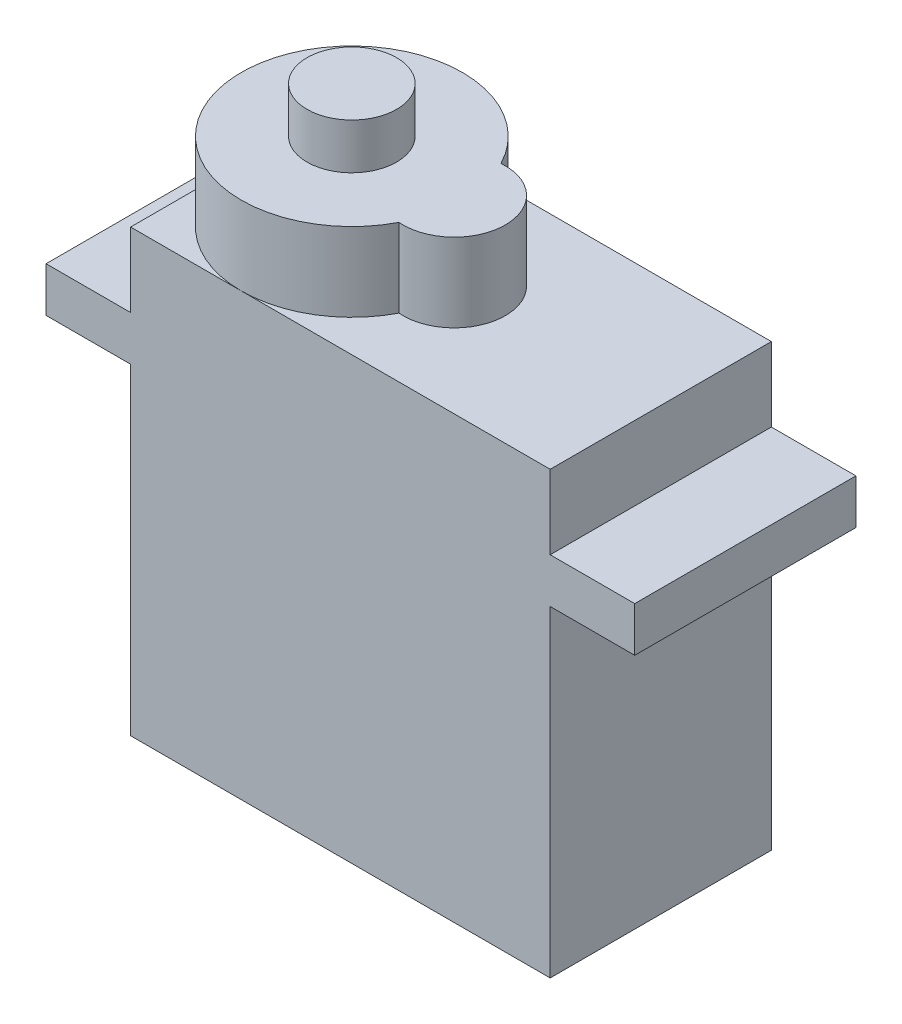
SolidWorks part; units mm, degrees
ref_plane "Front Plane" through (0, 0, 0) normal (0, 0, 1) x (1, 0, 0)
ref_plane "Top Plane" through (0, 0, 0) normal (0, 1, 0) x (1, 0, 0)
ref_plane "Right Plane" through (0, 0, 0) normal (1, 0, 0) x (0, 0, -1)
sketch "Sketch1" plane through (0, 0, 0) normal (0, 1, 0) x (1, 0, 0)
  line L1 (11.475, 6.05) -> (-11.475, 6.05)
  line L2 (11.475, 6.05) -> (11.475, -6.05)
  line L3 (11.475, -6.05) -> (-11.475, -6.05)
  line L4 (-11.475, 6.05) -> (-11.475, -6.05)
  line L5 (11.475, 6.05) -> (-11.475, -6.05) construction
  line L6 (11.475, -6.05) -> (-11.475, 6.05) construction
  point P0 (0, 0)
  dimension "D1" = 22.95
  dimension "D2" = 12.1
extrude "Boss-Extrude1" add sketch "Sketch1" along normal blind 24.1
sketch "Sketch2" plane through (0, 24.1, 0) normal (0, 1, 0) x (1, 0, 0)
  line L0 (-11.475, 6.05) -> (-11.475, -6.05) construction
  line L1 (-11.475, -6.05) -> (11.475, -6.05) construction
  line L2 (11.475, 6.05) -> (-11.475, 6.05) construction
  arc A0 (-0.0569, 2.7904) -> (-0.0569, -2.7904) centre (-5.425, 0) ccw
  arc A1 (-0.0569, -2.7904) -> (-0.0569, 2.7904) centre (0.175, 0) ccw
  point P10 (2.975, 0)
  dimension "D1" = 5.6
  dimension "D2" = 14.45
extrude "Boss-Extrude2" add sketch "Sketch2" along normal blind 4.3
ref_plane "Plane1" through (0, 20.05, 0) normal (0, 1, 0) x (1, 0, 0)
sketch "Sketch3" plane through (0, 20.05, 0) normal (0, 1, 0) x (1, 0, 0)
  line L0 (-11.475, -6.05) -> (-5.425, -6.05) construction
  line L1 (-11.475, 6.05) -> (-16.1, 6.05)
  line L2 (-11.475, 6.05) -> (-11.475, -6.05)
  line L3 (-11.475, -6.05) -> (-16.1, -6.05)
  line L4 (-16.1, 6.05) -> (-16.1, -6.05)
  line L5 (0, 10.0238) -> (0, -8.9788) construction
  line L6 (11.475, -6.05) -> (16.1, -6.05)
  line L7 (16.1, 6.05) -> (16.1, -6.05)
  line L8 (11.475, 6.05) -> (16.1, 6.05)
  line L9 (11.475, 6.05) -> (11.475, -6.05)
  dimension "D1" = 32.2
extrude "Boss-Extrude3" add sketch "Sketch3" against normal blind 2.45
sketch "Sketch4" plane through (0, 28.4, 0) normal (0, 1, 0) x (1, 0, 0)
  circle A0 centre (-5.425, 0) radius 2.45
  arc A1 (-5.425, 6.05) -> (-11.475, 0) centre (-5.425, 0) ccw construction
  dimension "D1" = 4.9
extrude "Boss-Extrude4" add sketch "Sketch4" along normal blind 2.5
sketch "Sketch5" plane through (-11.475, 0, 0) normal (-1, 0, 0) x (0, 0, 1)
  line L0 (-8.6549, 4) -> (8.54, 4) construction
  line L1 (0, 39.2141) -> (0, -11.4885) construction
  circle A0 centre (0, 4) radius 0.65
  circle A3 centre (1.34, 4) radius 0.65
  circle A4 centre (-1.34, 4) radius 0.65
  point P9 (1.3437, 4)
  dimension "D1" = 1.3
  dimension "D3" = 1.34
  dimension "D2" = 4
extrude "Boss-Extrude7" add sketch "Sketch5" along normal blind 3.9
